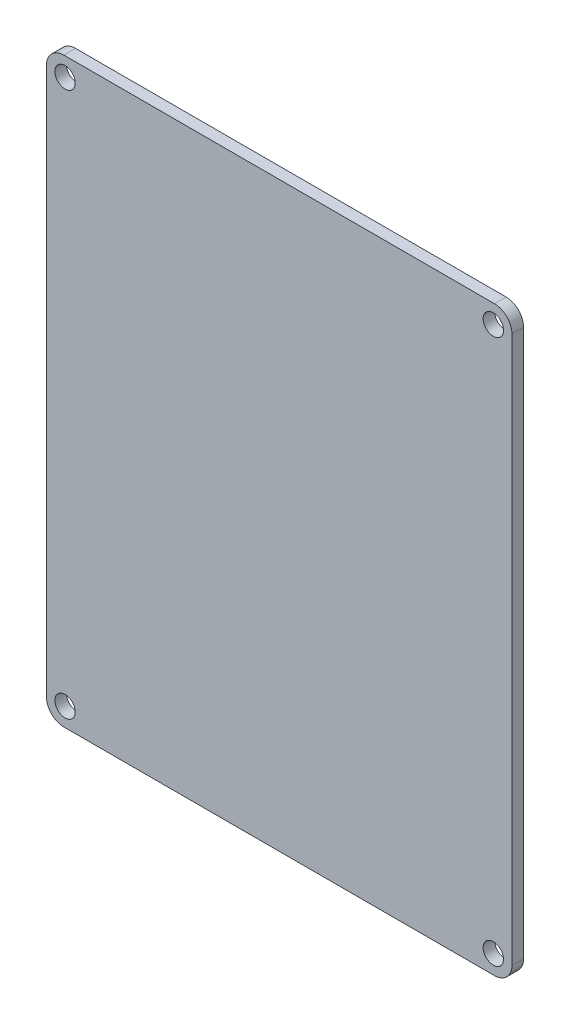
SolidWorks part; units mm, degrees
ref_plane "前视基准面" through (0, 0, 0) normal (0, 0, 1) x (1, 0, 0)
ref_plane "上视基准面" through (0, 0, 0) normal (0, 1, 0) x (1, 0, 0)
ref_plane "右视基准面" through (0, 0, 0) normal (1, 0, 0) x (0, 0, -1)
other "Configuration Table"
sketch "草图1" plane through (0, 0, 0) normal (0, 0, 1) x (1, 0, 0)
  line L1 (-37, 50) -> (37, 50)
  line L2 (-40, 47) -> (-40, -47)
  line L3 (-37, -50) -> (37, -50)
  line L4 (40, 47) -> (40, -47)
  line L5 (-40, 50) -> (40, -50) construction
  line L6 (-40, -50) -> (40, 50) construction
  arc A0 (37, -50) -> (40, -47) centre (37, -47) ccw
  arc A1 (-40, -47) -> (-37, -50) centre (-37, -47) ccw
  arc A2 (37, 50) -> (40, 47) centre (37, 47) cw
  arc A3 (-37, 50) -> (-40, 47) centre (-37, 47) ccw
  point P0 (0, 0)
  dimension "D3" = 3
  dimension "D1" = 80
  dimension "D2" = 100
extrude "凸台-拉伸1" add sketch "草图1" against normal blind 2
sketch "草图2" plane through (0, 0, 0) normal (0, 0, 1) x (1, 0, 0)
  line L0 (-40, 46.8) -> (40, 46.8)
  line L1 (-40, 47) -> (-40, -47) construction
  line L2 (40, -47) -> (40, 47) construction
  line L3 (-40, -46.8) -> (40, -46.8)
  line L4 (-36.8, 50) -> (-36.8, -50)
  line L5 (37, 50) -> (-37, 50) construction
  line L6 (-37, -50) -> (37, -50) construction
  line L7 (36.8, 50) -> (36.8, -50)
  circle A0 centre (-36.8, 46.8) radius 1.75
  circle A1 centre (36.8, 46.8) radius 1.75
  circle A2 centre (36.8, -46.8) radius 1.75
  circle A3 centre (-36.8, -46.8) radius 1.75
  point P16 (-36.8, 46.8)
  point P17 (-36.8, -46.8)
  point P18 (36.8, -46.8)
  point P19 (36.8, 46.8)
  dimension "D5" = 3.5
  dimension "D1" = 3.2
  dimension "D2" = 3.2
  dimension "D3" = 3.2
  dimension "D4" = 3.2
extrude "切除-拉伸1" cut sketch "草图2" against normal blind 2 contours L4 A0 L0 | L0 A0 L4 | L4 A0 L0 | L0 A0 L4 | L4 A3 L3 | L3 A3 L4 | L3 A3 L4 | L4 A3 L3 | L7 A2 L3 | L3 A2 L7 | L7 A2 L3 | L3 A2 L7 | L7 A1 L0 | L0 A1 L7 | L0 A1 L7 | L7 A1 L0
